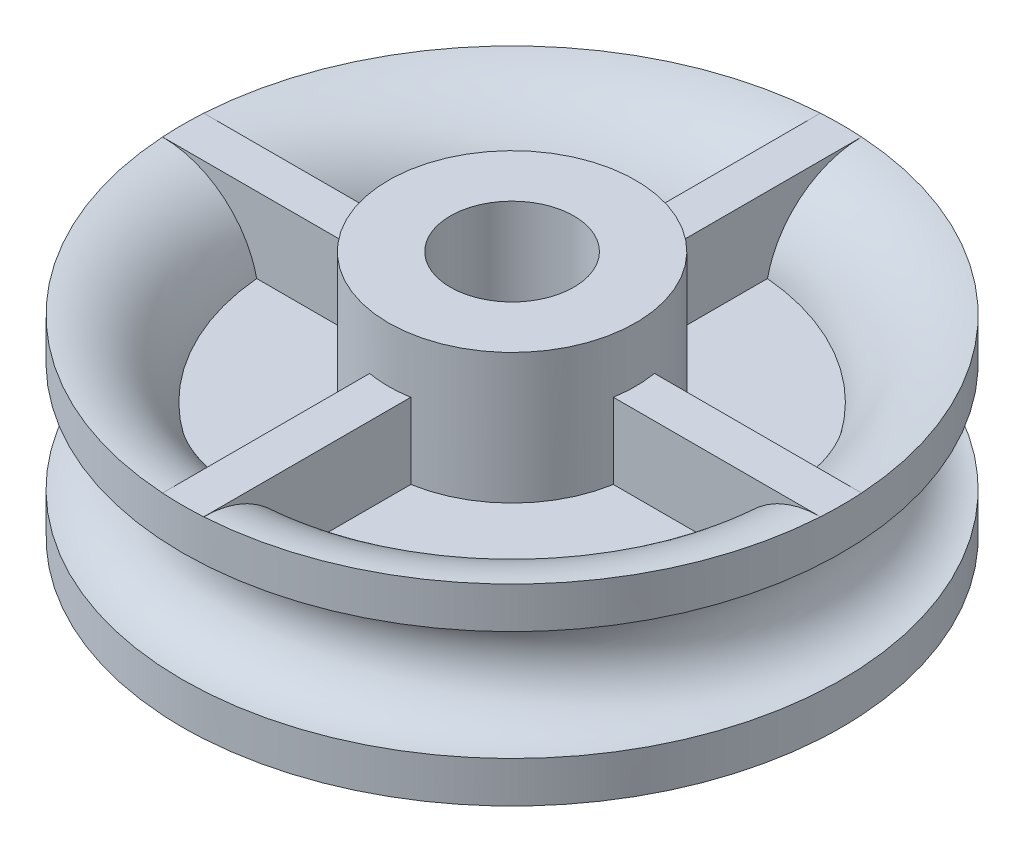
SolidWorks part; units mm, degrees
ref_plane "Front" through (0, 0, 0) normal (0, 0, 1) x (1, 0, 0)
ref_plane "Top" through (0, 0, 0) normal (0, 1, 0) x (1, 0, 0)
ref_plane "Right" through (0, 0, 0) normal (1, 0, 0) x (0, 0, -1)
sketch "Sketch1" plane through (0, 0, 0) normal (0, 0, 1) x (1, 0, 0)
  line L0 (-17.3427, 26.1536) -> (-17.3427, -14.8464)
  line L1 (-17.3427, -14.8464) -> (-26.3427, -14.8464)
  line L2 (-26.3427, -14.8464) -> (-26.3427, 4.1536)
  line L3 (-26.3427, 4.1536) -> (-42.6679, 4.1536)
  line L6 (-26.3427, 10.1536) -> (-26.3427, 26.1536)
  line L7 (-26.3427, 26.1536) -> (-17.3427, 26.1536)
  line L8 (-56.3427, 21.1536) -> (-56.3427, 15.1536)
  line L9 (-56.3427, -0.8464) -> (-56.3427, -6.8464)
  line L10 (-42.6679, 10.1536) -> (-26.3427, 10.1536)
  line L11 (-56.3427, 21.1536) -> (-26.3427, 21.1536)
  line L12 (-26.3427, 21.1536) -> (-26.3427, 18.1536)
  line L13 (-26.3427, 18.1536) -> (-47.6825, 18.1536)
  line L14 (-56.3427, -6.8464) -> (-26.3427, -6.8464)
  line L15 (-26.3427, -6.8464) -> (-26.3427, -3.8464)
  line L16 (-26.3427, -3.8464) -> (-47.6825, -3.8464)
  line L18 (-8.3427, 57.1522) -> (-8.3427, -46.6415) construction
  arc A0 (-56.3427, -6.8464) -> (-56.3427, 21.1536) centre (-56.3427, 7.1536) ccw
  arc A1 (-56.3427, -0.8464) -> (-56.3427, 15.1536) centre (-56.3427, 7.1536) ccw
revolve "Revolve2" add sketch "Sketch1" angle 360 about L18
sketch "Sketch5" plane through (0, 0, 0) normal (0, 0, 1) x (1, 0, 0)
  line L0 (-56.3427, 21.1536) -> (-26.3427, 21.1536) construction
  line L3 (-26.3427, 21.1536) -> (-56.3427, 21.1536)
rib "Rib9" sketch "Sketch5" sketch "Sketch5" thickness 6 extrusion direction parallel to sketch draft on no parameters "D1"=6
pattern_circular "CirPattern1" count 4 over 360 about axis through (-8.3427, 0, 0) along (0, 1, 0) of "Rib9"
ref_plane "Plane1" through (0, 7.1536, 0) normal (0, 1, 0) x (1, 0, 0)
mirror "Mirror1" about plane through (0, 7.1536, 0) normal (0, 1, 0) of bodies 105
